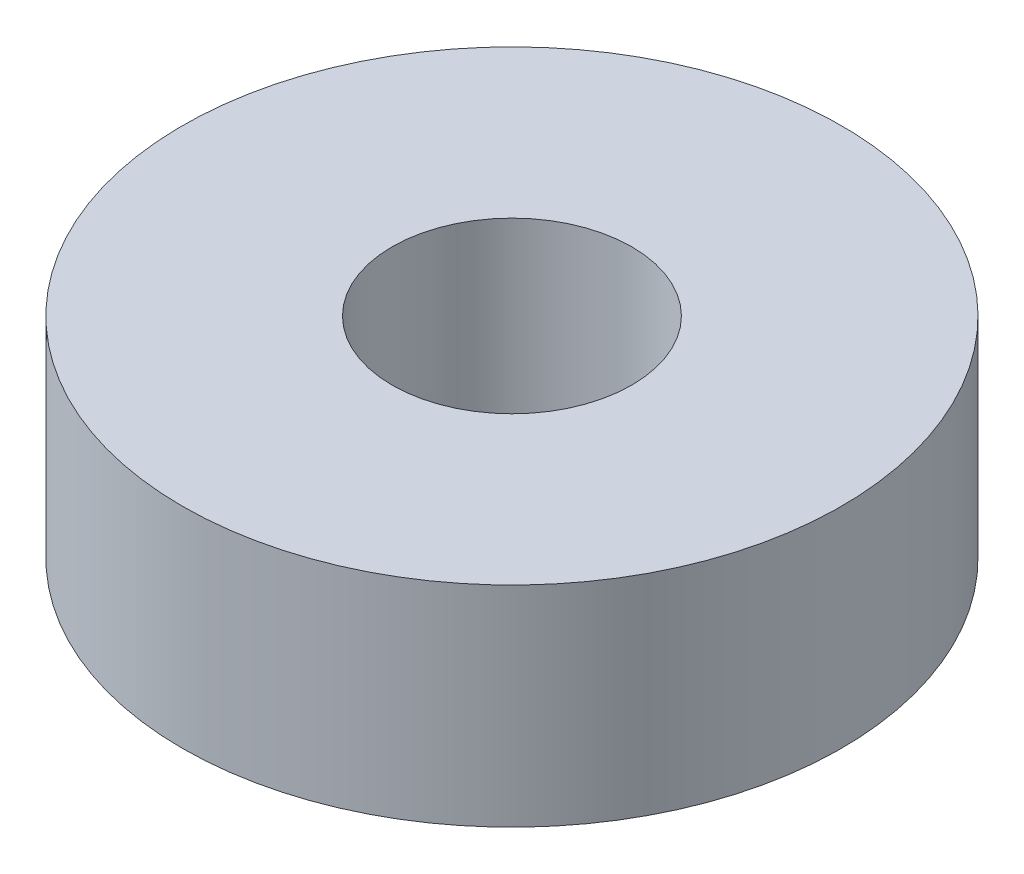
SolidWorks part; units mm, degrees
ref_plane "Front" through (0, 0, 0) normal (0, 0, 1) x (1, 0, 0)
ref_plane "Top" through (0, 0, 0) normal (0, 1, 0) x (1, 0, 0)
ref_plane "Right" through (0, 0, 0) normal (1, 0, 0) x (0, 0, -1)
sketch "Sketch1" plane through (0, 0, 0) normal (0, 1, 0) x (1, 0, 0)
  circle A0 centre (0, 0) radius 11
  circle A1 centre (0, 0) radius 4
  dimension "D1" = 8
  dimension "D2" = 22
extrude "Boss-Extrude1" add sketch "Sketch1" along normal blind 7
